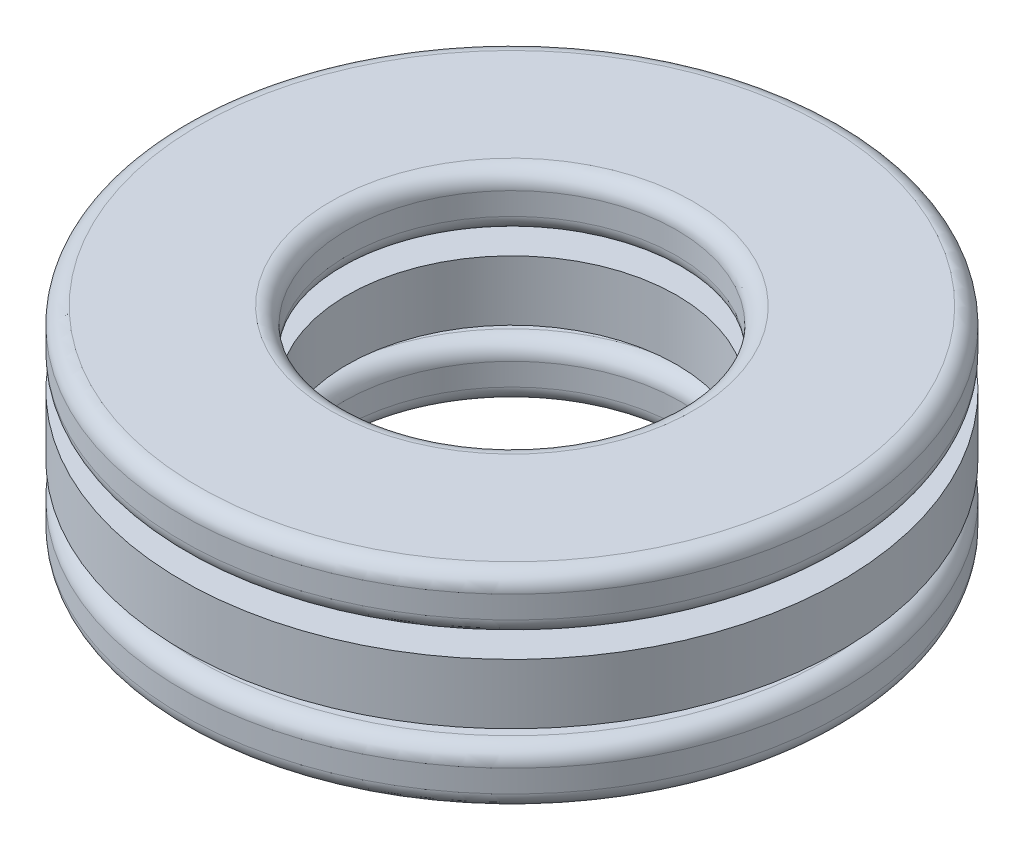
SolidWorks part; units mm, degrees
material "Alloy Steel"
ref_plane "Front Plane" through (0, 0, 0) normal (0, 0, 1) x (1, 0, 0)
ref_plane "Top Plane" through (0, 0, 0) normal (0, 1, 0) x (1, 0, 0)
ref_plane "Right Plane" through (0, 0, 0) normal (1, 0, 0) x (0, 0, -1)
sketch "Sketch1" plane through (0, 0, 0) normal (1, 0, 0) x (0, 0, -1)
  line L0 (-8, 0) -> (8, 0) construction
  line L1 (0, -3.5) -> (0, 3.5) construction
  line L2 (-8, 0.7292) -> (-4, 0.7292)
  line L3 (-8, 0.7292) -> (-8, -0.7292)
  line L4 (-8, -0.7292) -> (-4, -0.7292)
  line L5 (-4, 0.7292) -> (-4, -0.7292)
  line L6 (-6, 1.1667) -> (-6, -1.1667) construction
  line L7 (-6, 1.1667) -> (-6, 3.5) construction
  circle A0 centre (-6, 0) radius 1.1667 construction
  point P13 (-6, 0.7292)
  dimension "D1" = 2.3333
  dimension "OD" = 16
  dimension "Shaft Dia" = 8
  dimension "Th" = 7
  dimension "D2" = 1.4583
  dimension "D3" = 2.3333
revolve "Revolve1" add sketch "Sketch1" angle 360 about L1
sketch "Sketch3" plane through (0, 0, 0) normal (1, 0, 0) x (0, 0, -1)
  line L0 (-6, 1.1667) -> (-6, -1.1667)
  arc A0 (-6, 1.1667) -> (-6, -1.1667) centre (-6, 0) ccw
  circle A1 centre (-6, 0) radius 1.1667 construction
revolve "Cut-Revolve1" cut sketch "Sketch3" angle 360 about L0
sketch "Sketch2" plane through (0, 0, 0) normal (1, 0, 0) x (0, 0, -1)
  line L0 (-6, 1.1667) -> (-6, -1.1667)
  arc A0 (-6, 1.1667) -> (-6, -1.1667) centre (-6, 0) ccw
  circle A2 centre (-6, 0) radius 1.1667 construction
revolve "Revolve2" add sketch "Sketch2" angle 360 about L0
ref_axis "Axis1" through (0, 3.5, 0) along (0, -1, 0)
pattern_circular "CirPattern1" count 6 every 60 about axis through (0, 3.5, 0) along (0, -1, 0) of bodies 187
pattern_circular "CirPattern2" count 6 every 60 about axis through (0, 0, 0) along (0, 1, 0) of "Cut-Revolve1"
sketch "Sketch4" plane through (0, 0, 0) normal (1, 0, 0) x (0, 0, -1)
  line L0 (-8, 0.7292) -> (-8, -0.7292) construction
  line L2 (-8, 2.5) -> (-8, -2.5) construction
  line L3 (-7.6, 2.5) -> (-4.4, 2.5)
  line L4 (-4, 1.5583) -> (-4, 2.1)
  line L5 (-7.6, -2.5) -> (-4.5, -2.5)
  line L6 (-8, -2.1) -> (-8, -1.5583)
  line L8 (-7.6, 1.1583) -> (-4.4, 1.1583)
  line L10 (-4, 0.7292) -> (-4, -0.7292) construction
  line L11 (0, 0) -> (-8, 0) construction
  line L12 (-8, 0) -> (8, 0) construction
  line L13 (0, 0) -> (0, 2.5) construction
  line L14 (-8, 2.1) -> (-8, 1.5583)
  line L15 (-4.1, -1.5583) -> (-4.1, -2.1)
  line L16 (-7.6, -1.1583) -> (-4.5, -1.1583)
  arc A0 (-7.6, 2.5) -> (-8, 2.1) centre (-7.6, 2.1) ccw
  arc A1 (-4.4, 2.5) -> (-4, 2.1) centre (-4.4, 2.1) cw
  arc A2 (-4.4, 1.1583) -> (-4, 1.5583) centre (-4.4, 1.5583) ccw
  arc A3 (-4.5, -1.1583) -> (-4.1, -1.5583) centre (-4.5, -1.5583) cw
  arc A4 (-8, -1.5583) -> (-7.6, -1.1583) centre (-7.6, -1.5583) cw
  arc A5 (-7.6, -2.5) -> (-8, -2.1) centre (-7.6, -2.1) cw
  arc A6 (-7.6, 1.1583) -> (-8, 1.5583) centre (-7.6, 1.5583) cw
  arc A7 (-4.5, -2.5) -> (-4.1, -2.1) centre (-4.5, -2.1) ccw
  point P25 (-8, -1.1583)
  point P26 (-8.5, 0.0333)
  point P29 (-8.5, -0.0333)
  dimension "r" = 0.4
  dimension "D5" = 16
  dimension "D1" = 1.3417
  dimension "Ht" = 5
  dimension "D3" = 8
  dimension "dia2" = 8.2
  dimension "dia1" = 16
revolve "Revolve3" add sketch "Sketch4" angle 360 about L1
equation "\"D1@Sketch1\" = \"Th@Sketch1\"/3"
equation "\"D2@Sketch1\" = \"D1@Sketch1\"*.625"
equation "\"Balls@CirPattern1\" = \"OD@Sketch1\"*.375"
equation "\"Angle@CirPattern1\" = 360/\"Balls@CirPattern1\""
equation "\"D1@CirPattern2\" = \"Balls@CirPattern1\""
equation "\"D2@CirPattern2\" = \"Angle@CirPattern1\""
equation "\"D1@Sketch4\" = \"D3@Sketch1\"*.575"
